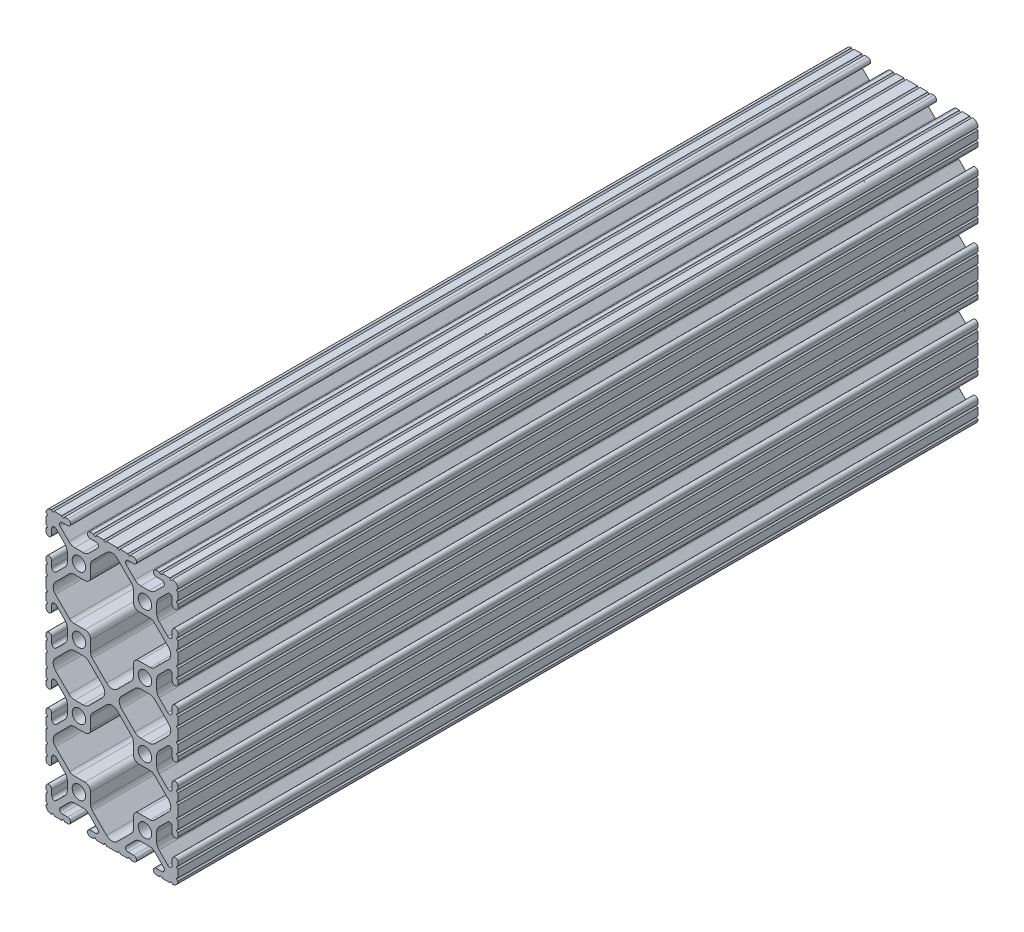
SolidWorks part; units mm, degrees
ref_plane "Front Plane" through (0, 0, 0) normal (0, 0, 1) x (1, 0, 0)
ref_plane "Top Plane" through (0, 0, 0) normal (0, 1, 0) x (1, 0, 0)
ref_plane "Right Plane" through (0, 0, 0) normal (1, 0, 0) x (0, 0, -1)
sketch "Sketch1" plane through (0, 0, 0) normal (0, 0, 1) x (1, 0, 0)
  line L0 (2.286, 55.2958) -> (-2.0184, 55.2958)
  line L1 (-3.5809, 55.943) -> (-9.0725, 61.4345)
  line L2 (-9.0725, 65.5655) -> (-3.5809, 71.057)
  line L3 (-2.0184, 71.7042) -> (2.286, 71.7042)
  line L4 (4.4958, 73.914) -> (4.4958, 78.2184)
  line L5 (5.143, 79.7809) -> (10.6345, 85.2725)
  line L6 (14.7655, 85.2725) -> (20.257, 79.7809)
  line L7 (20.9042, 78.2184) -> (20.9042, 73.914)
  line L8 (23.114, 71.7042) -> (27.4184, 71.7042)
  line L9 (28.9809, 71.057) -> (34.4725, 65.5655)
  line L10 (34.4725, 61.4345) -> (28.9809, 55.943)
  line L11 (27.4184, 55.2958) -> (23.114, 55.2958)
  line L12 (20.9042, 53.086) -> (20.9042, 48.7816)
  line L13 (20.257, 47.2191) -> (14.7655, 41.7275)
  line L14 (10.6345, 41.7275) -> (5.143, 47.2191)
  line L15 (4.4958, 48.7816) -> (4.4958, 53.086)
  line L16 (4.4958, 23.114) -> (4.4958, 27.4184)
  line L17 (5.143, 28.9809) -> (10.6345, 34.4725)
  line L18 (14.7655, 34.4725) -> (20.257, 28.9809)
  line L19 (20.9042, 27.4184) -> (20.9042, 23.114)
  line L20 (23.114, 20.9042) -> (27.4184, 20.9042)
  line L21 (28.9809, 20.257) -> (34.4725, 14.7655)
  line L22 (34.4725, 10.6345) -> (28.9809, 5.143)
  line L23 (27.4184, 4.4958) -> (23.114, 4.4958)
  line L24 (20.9042, 2.286) -> (20.9042, -2.0184)
  line L25 (20.257, -3.5809) -> (14.7655, -9.0725)
  line L26 (10.6345, -9.0725) -> (5.143, -3.5809)
  line L27 (4.4958, -2.0184) -> (4.4958, 2.286)
  line L28 (2.286, 4.4958) -> (-2.0184, 4.4958)
  line L29 (-3.5809, 5.143) -> (-9.0725, 10.6345)
  line L30 (-9.0725, 14.7655) -> (-3.5809, 20.257)
  line L31 (-2.0184, 20.9042) -> (2.286, 20.9042)
  line L32 (27.0186, 29.8958) -> (23.7824, 29.8958)
  line L33 (21.5373, 30.8258) -> (16.3286, 36.0346)
  line L34 (16.3286, 40.1654) -> (21.5373, 45.3742)
  line L35 (23.7824, 46.3042) -> (27.0186, 46.3042)
  line L36 (29.2636, 45.3743) -> (34.4725, 40.1655)
  line L37 (34.4725, 36.0345) -> (29.2636, 30.8257)
  line L38 (1.6176, 29.8958) -> (-1.6186, 29.8958)
  line L39 (-3.8636, 30.8257) -> (-9.0725, 36.0345)
  line L40 (-9.0725, 40.1655) -> (-3.8636, 45.3743)
  line L41 (-1.6186, 46.3042) -> (1.6176, 46.3042)
  line L42 (3.8627, 45.3742) -> (9.0714, 40.1654)
  line L43 (9.0714, 36.0346) -> (3.8627, 30.8258)
  line L44 (-12.7, 40.2336) -> (-12.7, 35.9664)
  line L45 (-12.7, 34.9504) -> (-12.7, 32.004)
  line L46 (-12.7, 30.988) -> (-12.7, 29.7434)
  line L47 (-10.4902, 29.7434) -> (-10.4902, 31.8743)
  line L48 (-8.7558, 32.5927) -> (-5.4258, 29.2627)
  line L49 (-4.4958, 27.0176) -> (-4.4958, 23.7824)
  line L50 (-5.4258, 21.5373) -> (-8.7558, 18.2073)
  line L51 (-10.4902, 18.9257) -> (-10.4902, 21.0566)
  line L52 (-12.7, 21.0566) -> (-12.7, 19.812)
  line L53 (-12.7, 18.796) -> (-12.7, 15.8496)
  line L54 (-12.7, 14.8336) -> (-12.7, 10.5664)
  line L55 (-12.7, 9.5504) -> (-12.7, 6.604)
  line L56 (-12.7, 5.588) -> (-12.7, 4.3434)
  line L57 (-10.4902, 4.3434) -> (-10.4902, 6.4743)
  line L58 (-8.7558, 7.1927) -> (-5.4258, 3.8627)
  line L59 (-4.4958, 1.6176) -> (-4.4958, -1.6176)
  line L60 (-5.4258, -3.8627) -> (-8.7558, -7.1927)
  line L61 (-10.4902, -6.4743) -> (-10.4902, -4.3434)
  line L62 (-12.7, -4.3434) -> (-12.7, -5.588)
  line L63 (-12.7, -6.604) -> (-12.7, -9.5504)
  line L64 (-9.5504, -12.7) -> (-6.604, -12.7)
  line L65 (-5.588, -12.7) -> (-4.3434, -12.7)
  line L66 (-4.3434, -10.4902) -> (-6.4743, -10.4902)
  line L67 (-7.1927, -8.7558) -> (-3.8627, -5.4258)
  line L68 (-1.6176, -4.4958) -> (1.6176, -4.4958)
  line L69 (3.8627, -5.4258) -> (7.1927, -8.7558)
  line L70 (6.4743, -10.4902) -> (4.3434, -10.4902)
  line L71 (4.3434, -12.7) -> (5.588, -12.7)
  line L72 (6.604, -12.7) -> (9.5504, -12.7)
  line L73 (10.5664, -12.7) -> (14.8336, -12.7)
  line L74 (15.8496, -12.7) -> (18.796, -12.7)
  line L75 (19.812, -12.7) -> (21.0566, -12.7)
  line L76 (21.0566, -10.4902) -> (18.9257, -10.4902)
  line L77 (18.2073, -8.7558) -> (21.5373, -5.4258)
  line L78 (23.7824, -4.4958) -> (27.0176, -4.4958)
  line L79 (29.2627, -5.4258) -> (32.5927, -8.7558)
  line L80 (31.8743, -10.4902) -> (29.7434, -10.4902)
  line L81 (29.7434, -12.7) -> (30.988, -12.7)
  line L82 (32.004, -12.7) -> (34.9504, -12.7)
  line L83 (38.1, -9.5504) -> (38.1, -6.604)
  line L84 (38.1, -5.588) -> (38.1, -4.3434)
  line L85 (35.8902, -4.3434) -> (35.8902, -6.4743)
  line L86 (34.1558, -7.1927) -> (30.8258, -3.8627)
  line L87 (29.8958, -1.6176) -> (29.8958, 1.6176)
  line L88 (30.8258, 3.8627) -> (34.1558, 7.1927)
  line L89 (35.8902, 6.4743) -> (35.8902, 4.3434)
  line L90 (38.1, 4.3434) -> (38.1, 5.588)
  line L91 (38.1, 6.604) -> (38.1, 9.5504)
  line L92 (38.1, 10.5664) -> (38.1, 14.8336)
  line L93 (38.1, 15.8496) -> (38.1, 18.796)
  line L94 (38.1, 19.812) -> (38.1, 21.0566)
  line L95 (35.8902, 21.0566) -> (35.8902, 18.9257)
  line L96 (34.1558, 18.2073) -> (30.8258, 21.5373)
  line L97 (29.8958, 23.7824) -> (29.8958, 27.0176)
  line L98 (30.8258, 29.2627) -> (34.1558, 32.5927)
  line L99 (35.8902, 31.8743) -> (35.8902, 29.7434)
  line L100 (38.1, 29.7434) -> (38.1, 30.988)
  line L101 (38.1, 32.004) -> (38.1, 34.9504)
  line L102 (38.1, 35.9664) -> (38.1, 40.2336)
  line L103 (38.1, 41.2496) -> (38.1, 44.196)
  line L104 (38.1, 45.212) -> (38.1, 46.4566)
  line L105 (35.8902, 46.4566) -> (35.8902, 44.3257)
  line L106 (34.1558, 43.6073) -> (30.8258, 46.9373)
  line L107 (29.8958, 49.1824) -> (29.8958, 52.4176)
  line L108 (30.8258, 54.6627) -> (34.1558, 57.9927)
  line L109 (35.8902, 57.2743) -> (35.8902, 55.1434)
  line L110 (38.1, 55.1434) -> (38.1, 56.388)
  line L111 (38.1, 57.404) -> (38.1, 60.3504)
  line L112 (38.1, 61.3664) -> (38.1, 65.6336)
  line L113 (38.1, 66.6496) -> (38.1, 69.596)
  line L114 (38.1, 70.612) -> (38.1, 71.8566)
  line L115 (35.8902, 71.8566) -> (35.8902, 69.7257)
  line L116 (34.1558, 69.0073) -> (30.8258, 72.3373)
  line L117 (29.8958, 74.5824) -> (29.8958, 77.8176)
  line L118 (30.8258, 80.0627) -> (34.1558, 83.3927)
  line L119 (35.8902, 82.6743) -> (35.8902, 80.5434)
  line L120 (38.1, 80.5434) -> (38.1, 81.788)
  line L121 (38.1, 82.804) -> (38.1, 85.7504)
  line L122 (34.9504, 88.9) -> (32.004, 88.9)
  line L123 (30.988, 88.9) -> (29.7434, 88.9)
  line L124 (29.7434, 86.6902) -> (31.8743, 86.6902)
  line L125 (32.5927, 84.9558) -> (29.2627, 81.6258)
  line L126 (27.0176, 80.6958) -> (23.7824, 80.6958)
  line L127 (21.5373, 81.6258) -> (18.2073, 84.9558)
  line L128 (18.9257, 86.6902) -> (21.0566, 86.6902)
  line L129 (21.0566, 88.9) -> (19.812, 88.9)
  line L130 (18.796, 88.9) -> (15.8496, 88.9)
  line L131 (14.8336, 88.9) -> (10.5664, 88.9)
  line L132 (9.5504, 88.9) -> (6.604, 88.9)
  line L133 (5.588, 88.9) -> (4.3434, 88.9)
  line L134 (4.3434, 86.6902) -> (6.4743, 86.6902)
  line L135 (7.1927, 84.9558) -> (3.8627, 81.6258)
  line L136 (1.6176, 80.6958) -> (-1.6176, 80.6958)
  line L137 (-3.8627, 81.6258) -> (-7.1927, 84.9558)
  line L138 (-6.4743, 86.6902) -> (-4.3434, 86.6902)
  line L139 (-4.3434, 88.9) -> (-5.588, 88.9)
  line L140 (-6.604, 88.9) -> (-9.5504, 88.9)
  line L141 (-12.7, 85.7504) -> (-12.7, 82.804)
  line L142 (-12.7, 81.788) -> (-12.7, 80.5434)
  line L143 (-10.4902, 80.5434) -> (-10.4902, 82.6743)
  line L144 (-8.7558, 83.3927) -> (-5.4258, 80.0627)
  line L145 (-4.4958, 77.8176) -> (-4.4958, 74.5824)
  line L146 (-5.4258, 72.3373) -> (-8.7558, 69.0073)
  line L147 (-10.4902, 69.7257) -> (-10.4902, 71.8566)
  line L148 (-12.7, 71.8566) -> (-12.7, 70.612)
  line L149 (-12.7, 69.596) -> (-12.7, 66.6496)
  line L150 (-12.7, 65.6336) -> (-12.7, 61.3664)
  line L151 (-12.7, 60.3504) -> (-12.7, 57.404)
  line L152 (-12.7, 56.388) -> (-12.7, 55.1434)
  line L153 (-10.4902, 55.1434) -> (-10.4902, 57.2743)
  line L154 (-8.7558, 57.9927) -> (-5.4258, 54.6627)
  line L155 (-4.4958, 52.4176) -> (-4.4958, 49.1824)
  line L156 (-5.4258, 46.9373) -> (-8.7558, 43.6073)
  line L157 (-10.4902, 44.3257) -> (-10.4902, 46.4566)
  line L158 (-12.7, 46.4566) -> (-12.7, 45.212)
  line L159 (-12.7, 44.196) -> (-12.7, 41.2496)
  arc A0 (4.4958, 53.086) -> (2.286, 55.2958) centre (2.286, 53.086) ccw
  arc A1 (-3.5809, 55.943) -> (-2.0184, 55.2958) centre (-2.0184, 57.5056) ccw
  arc A2 (-9.0725, 65.5655) -> (-9.0725, 61.4345) centre (-7.0071, 63.5) ccw
  arc A3 (-2.0184, 71.7042) -> (-3.5809, 71.057) centre (-2.0184, 69.4944) ccw
  arc A4 (2.286, 71.7042) -> (4.4958, 73.914) centre (2.286, 73.914) ccw
  arc A5 (5.143, 79.7809) -> (4.4958, 78.2184) centre (6.7056, 78.2184) ccw
  arc A6 (14.7655, 85.2725) -> (10.6345, 85.2725) centre (12.7, 83.2071) ccw
  arc A7 (20.9042, 78.2184) -> (20.257, 79.7809) centre (18.6944, 78.2184) ccw
  arc A8 (20.9042, 73.914) -> (23.114, 71.7042) centre (23.114, 73.914) ccw
  arc A9 (28.9809, 71.057) -> (27.4184, 71.7042) centre (27.4184, 69.4944) ccw
  arc A10 (34.4725, 61.4345) -> (34.4725, 65.5655) centre (32.4071, 63.5) ccw
  arc A11 (27.4184, 55.2958) -> (28.9809, 55.943) centre (27.4184, 57.5056) ccw
  arc A12 (23.114, 55.2958) -> (20.9042, 53.086) centre (23.114, 53.086) ccw
  arc A13 (20.257, 47.2191) -> (20.9042, 48.7816) centre (18.6944, 48.7816) ccw
  arc A14 (10.6345, 41.7275) -> (14.7655, 41.7275) centre (12.7, 43.7929) ccw
  arc A15 (4.4958, 48.7816) -> (5.143, 47.2191) centre (6.7056, 48.7816) ccw
  arc A16 (2.286, 20.9042) -> (4.4958, 23.114) centre (2.286, 23.114) ccw
  arc A17 (5.143, 28.9809) -> (4.4958, 27.4184) centre (6.7056, 27.4184) ccw
  arc A18 (14.7655, 34.4725) -> (10.6345, 34.4725) centre (12.7, 32.4071) ccw
  arc A19 (20.9042, 27.4184) -> (20.257, 28.9809) centre (18.6944, 27.4184) ccw
  arc A20 (20.9042, 23.114) -> (23.114, 20.9042) centre (23.114, 23.114) ccw
  arc A21 (28.9809, 20.257) -> (27.4184, 20.9042) centre (27.4184, 18.6944) ccw
  arc A22 (34.4725, 10.6345) -> (34.4725, 14.7655) centre (32.4071, 12.7) ccw
  arc A23 (27.4184, 4.4958) -> (28.9809, 5.143) centre (27.4184, 6.7056) ccw
  arc A24 (23.114, 4.4958) -> (20.9042, 2.286) centre (23.114, 2.286) ccw
  arc A25 (20.257, -3.5809) -> (20.9042, -2.0184) centre (18.6944, -2.0184) ccw
  arc A26 (10.6345, -9.0725) -> (14.7655, -9.0725) centre (12.7, -7.0071) ccw
  arc A27 (4.4958, -2.0184) -> (5.143, -3.5809) centre (6.7056, -2.0184) ccw
  arc A28 (4.4958, 2.286) -> (2.286, 4.4958) centre (2.286, 2.286) ccw
  arc A29 (-3.5809, 5.143) -> (-2.0184, 4.4958) centre (-2.0184, 6.7056) ccw
  arc A30 (-9.0725, 14.7655) -> (-9.0725, 10.6345) centre (-7.0071, 12.7) ccw
  arc A31 (-2.0184, 20.9042) -> (-3.5809, 20.257) centre (-2.0184, 18.6944) ccw
  arc A32 (27.0186, 29.8958) -> (29.2636, 30.8257) centre (27.0186, 33.0708) ccw
  arc A33 (21.5373, 30.8258) -> (23.7824, 29.8958) centre (23.7824, 33.0708) ccw
  arc A34 (16.3286, 40.1654) -> (16.3286, 36.0346) centre (18.3941, 38.1) ccw
  arc A35 (23.7824, 46.3042) -> (21.5373, 45.3742) centre (23.7824, 43.1292) ccw
  arc A36 (29.2636, 45.3743) -> (27.0186, 46.3042) centre (27.0186, 43.1292) ccw
  arc A37 (34.4725, 36.0345) -> (34.4725, 40.1655) centre (32.4071, 38.1) ccw
  arc A38 (1.6176, 29.8958) -> (3.8627, 30.8258) centre (1.6176, 33.0708) ccw
  arc A39 (-3.8636, 30.8257) -> (-1.6186, 29.8958) centre (-1.6186, 33.0708) ccw
  arc A40 (-9.0725, 40.1655) -> (-9.0725, 36.0345) centre (-7.0071, 38.1) ccw
  arc A41 (-1.6186, 46.3042) -> (-3.8636, 45.3743) centre (-1.6186, 43.1292) ccw
  arc A42 (3.8627, 45.3742) -> (1.6176, 46.3042) centre (1.6176, 43.1292) ccw
  arc A43 (9.0714, 36.0346) -> (9.0714, 40.1654) centre (7.0059, 38.1) ccw
  circle A44 centre (25.4, 76.2) radius 2.6035
  circle A45 centre (0, 76.2) radius 2.6035
  circle A46 centre (25.4, 50.8) radius 2.6035
  circle A47 centre (0, 50.8) radius 2.6035
  circle A48 centre (25.4, 0) radius 2.6035
  circle A49 centre (0, 0) radius 2.6035
  circle A50 centre (25.4, 25.4) radius 2.6035
  circle A51 centre (0, 25.4) radius 2.6035
  arc A52 (-12.7, 34.9504) -> (-12.7, 35.9664) centre (-12.7, 35.4584) ccw
  arc A53 (-12.7, 30.988) -> (-12.7, 32.004) centre (-12.7, 31.496) ccw
  arc A54 (-12.7, 29.7434) -> (-10.4902, 29.7434) centre (-11.5951, 29.7434) ccw
  arc A55 (-8.7558, 32.5927) -> (-10.4902, 31.8743) centre (-9.4742, 31.8743) ccw
  arc A56 (-4.4958, 27.0176) -> (-5.4258, 29.2627) centre (-7.6708, 27.0176) ccw
  arc A57 (-5.4258, 21.5373) -> (-4.4958, 23.7824) centre (-7.6708, 23.7824) ccw
  arc A58 (-10.4902, 18.9257) -> (-8.7558, 18.2073) centre (-9.4742, 18.9257) ccw
  arc A59 (-10.4902, 21.0566) -> (-12.7, 21.0566) centre (-11.5951, 21.0566) ccw
  arc A60 (-12.7, 18.796) -> (-12.7, 19.812) centre (-12.7, 19.304) ccw
  arc A61 (-12.7, 14.8336) -> (-12.7, 15.8496) centre (-12.7, 15.3416) ccw
  arc A62 (-12.7, 9.5504) -> (-12.7, 10.5664) centre (-12.7, 10.0584) ccw
  arc A63 (-12.7, 5.588) -> (-12.7, 6.604) centre (-12.7, 6.096) ccw
  arc A64 (-12.7, 4.3434) -> (-10.4902, 4.3434) centre (-11.5951, 4.3434) ccw
  arc A65 (-8.7558, 7.1927) -> (-10.4902, 6.4743) centre (-9.4742, 6.4743) ccw
  arc A66 (-4.4958, 1.6176) -> (-5.4258, 3.8627) centre (-7.6708, 1.6176) ccw
  arc A67 (-5.4258, -3.8627) -> (-4.4958, -1.6176) centre (-7.6708, -1.6176) ccw
  arc A68 (-10.4902, -6.4743) -> (-8.7558, -7.1927) centre (-9.4742, -6.4743) ccw
  arc A69 (-10.4902, -4.3434) -> (-12.7, -4.3434) centre (-11.5951, -4.3434) ccw
  arc A70 (-12.7, -6.604) -> (-12.7, -5.588) centre (-12.7, -6.096) ccw
  arc A71 (-12.6998, -10.5664) -> (-12.7, -9.5504) centre (-12.7, -10.0584) ccw
  arc A72 (-12.6998, -10.5664) -> (-10.5664, -12.6998) centre (-10.5918, -10.5918) ccw
  arc A73 (-9.5504, -12.7) -> (-10.5664, -12.6998) centre (-10.0584, -12.7) ccw
  arc A74 (-5.588, -12.7) -> (-6.604, -12.7) centre (-6.096, -12.7) ccw
  arc A75 (-4.3434, -12.7) -> (-4.3434, -10.4902) centre (-4.3434, -11.5951) ccw
  arc A76 (-7.1927, -8.7558) -> (-6.4743, -10.4902) centre (-6.4743, -9.4742) ccw
  arc A77 (-1.6176, -4.4958) -> (-3.8627, -5.4258) centre (-1.6176, -7.6708) ccw
  arc A78 (3.8627, -5.4258) -> (1.6176, -4.4958) centre (1.6176, -7.6708) ccw
  arc A79 (6.4743, -10.4902) -> (7.1927, -8.7558) centre (6.4743, -9.4742) ccw
  arc A80 (4.3434, -10.4902) -> (4.3434, -12.7) centre (4.3434, -11.5951) ccw
  arc A81 (6.604, -12.7) -> (5.588, -12.7) centre (6.096, -12.7) ccw
  arc A82 (10.5664, -12.7) -> (9.5504, -12.7) centre (10.0584, -12.7) ccw
  arc A83 (15.8496, -12.7) -> (14.8336, -12.7) centre (15.3416, -12.7) ccw
  arc A84 (19.812, -12.7) -> (18.796, -12.7) centre (19.304, -12.7) ccw
  arc A85 (21.0566, -12.7) -> (21.0566, -10.4902) centre (21.0566, -11.5951) ccw
  arc A86 (18.2073, -8.7558) -> (18.9257, -10.4902) centre (18.9257, -9.4742) ccw
  arc A87 (23.7824, -4.4958) -> (21.5373, -5.4258) centre (23.7824, -7.6708) ccw
  arc A88 (29.2627, -5.4258) -> (27.0176, -4.4958) centre (27.0176, -7.6708) ccw
  arc A89 (31.8743, -10.4902) -> (32.5927, -8.7558) centre (31.8743, -9.4742) ccw
  arc A90 (29.7434, -10.4902) -> (29.7434, -12.7) centre (29.7434, -11.5951) ccw
  arc A91 (32.004, -12.7) -> (30.988, -12.7) centre (31.496, -12.7) ccw
  arc A92 (35.9664, -12.6998) -> (34.9504, -12.7) centre (35.4584, -12.7) ccw
  arc A93 (35.9664, -12.6998) -> (38.0998, -10.5664) centre (35.9918, -10.5918) ccw
  arc A94 (38.1, -9.5504) -> (38.0998, -10.5664) centre (38.1, -10.0584) ccw
  arc A95 (38.1, -5.588) -> (38.1, -6.604) centre (38.1, -6.096) ccw
  arc A96 (38.1, -4.3434) -> (35.8902, -4.3434) centre (36.9951, -4.3434) ccw
  arc A97 (34.1558, -7.1927) -> (35.8902, -6.4743) centre (34.8742, -6.4743) ccw
  arc A98 (29.8958, -1.6176) -> (30.8258, -3.8627) centre (33.0708, -1.6176) ccw
  arc A99 (30.8258, 3.8627) -> (29.8958, 1.6176) centre (33.0708, 1.6176) ccw
  arc A100 (35.8902, 6.4743) -> (34.1558, 7.1927) centre (34.8742, 6.4743) ccw
  arc A101 (35.8902, 4.3434) -> (38.1, 4.3434) centre (36.9951, 4.3434) ccw
  arc A102 (38.1, 6.604) -> (38.1, 5.588) centre (38.1, 6.096) ccw
  arc A103 (38.1, 10.5664) -> (38.1, 9.5504) centre (38.1, 10.0584) ccw
  arc A104 (38.1, 15.8496) -> (38.1, 14.8336) centre (38.1, 15.3416) ccw
  arc A105 (38.1, 19.812) -> (38.1, 18.796) centre (38.1, 19.304) ccw
  arc A106 (38.1, 21.0566) -> (35.8902, 21.0566) centre (36.9951, 21.0566) ccw
  arc A107 (34.1558, 18.2073) -> (35.8902, 18.9257) centre (34.8742, 18.9257) ccw
  arc A108 (29.8958, 23.7824) -> (30.8258, 21.5373) centre (33.0708, 23.7824) ccw
  arc A109 (30.8258, 29.2627) -> (29.8958, 27.0176) centre (33.0708, 27.0176) ccw
  arc A110 (35.8902, 31.8743) -> (34.1558, 32.5927) centre (34.8742, 31.8743) ccw
  arc A111 (35.8902, 29.7434) -> (38.1, 29.7434) centre (36.9951, 29.7434) ccw
  arc A112 (38.1, 32.004) -> (38.1, 30.988) centre (38.1, 31.496) ccw
  arc A113 (38.1, 35.9664) -> (38.1, 34.9504) centre (38.1, 35.4584) ccw
  arc A114 (38.1, 41.2496) -> (38.1, 40.2336) centre (38.1, 40.7416) ccw
  arc A115 (38.1, 45.212) -> (38.1, 44.196) centre (38.1, 44.704) ccw
  arc A116 (38.1, 46.4566) -> (35.8902, 46.4566) centre (36.9951, 46.4566) ccw
  arc A117 (34.1558, 43.6073) -> (35.8902, 44.3257) centre (34.8742, 44.3257) ccw
  arc A118 (29.8958, 49.1824) -> (30.8258, 46.9373) centre (33.0708, 49.1824) ccw
  arc A119 (30.8258, 54.6627) -> (29.8958, 52.4176) centre (33.0708, 52.4176) ccw
  arc A120 (35.8902, 57.2743) -> (34.1558, 57.9927) centre (34.8742, 57.2743) ccw
  arc A121 (35.8902, 55.1434) -> (38.1, 55.1434) centre (36.9951, 55.1434) ccw
  arc A122 (38.1, 57.404) -> (38.1, 56.388) centre (38.1, 56.896) ccw
  arc A123 (38.1, 61.3664) -> (38.1, 60.3504) centre (38.1, 60.8584) ccw
  arc A124 (38.1, 66.6496) -> (38.1, 65.6336) centre (38.1, 66.1416) ccw
  arc A125 (38.1, 70.612) -> (38.1, 69.596) centre (38.1, 70.104) ccw
  arc A126 (38.1, 71.8566) -> (35.8902, 71.8566) centre (36.9951, 71.8566) ccw
  arc A127 (34.1558, 69.0073) -> (35.8902, 69.7257) centre (34.8742, 69.7257) ccw
  arc A128 (29.8958, 74.5824) -> (30.8258, 72.3373) centre (33.0708, 74.5824) ccw
  arc A129 (30.8258, 80.0627) -> (29.8958, 77.8176) centre (33.0708, 77.8176) ccw
  arc A130 (35.8902, 82.6743) -> (34.1558, 83.3927) centre (34.8742, 82.6743) ccw
  arc A131 (35.8902, 80.5434) -> (38.1, 80.5434) centre (36.9951, 80.5434) ccw
  arc A132 (38.1, 82.804) -> (38.1, 81.788) centre (38.1, 82.296) ccw
  arc A133 (38.0998, 86.7664) -> (38.1, 85.7504) centre (38.1, 86.2584) ccw
  arc A134 (38.0998, 86.7664) -> (35.9664, 88.8998) centre (35.9918, 86.7918) ccw
  arc A135 (34.9504, 88.9) -> (35.9664, 88.8998) centre (35.4584, 88.9) ccw
  arc A136 (30.988, 88.9) -> (32.004, 88.9) centre (31.496, 88.9) ccw
  arc A137 (29.7434, 88.9) -> (29.7434, 86.6902) centre (29.7434, 87.7951) ccw
  arc A138 (32.5927, 84.9558) -> (31.8743, 86.6902) centre (31.8743, 85.6742) ccw
  arc A139 (27.0176, 80.6958) -> (29.2627, 81.6258) centre (27.0176, 83.8708) ccw
  arc A140 (21.5373, 81.6258) -> (23.7824, 80.6958) centre (23.7824, 83.8708) ccw
  arc A141 (18.9257, 86.6902) -> (18.2073, 84.9558) centre (18.9257, 85.6742) ccw
  arc A142 (21.0566, 86.6902) -> (21.0566, 88.9) centre (21.0566, 87.7951) ccw
  arc A143 (18.796, 88.9) -> (19.812, 88.9) centre (19.304, 88.9) ccw
  arc A144 (14.8336, 88.9) -> (15.8496, 88.9) centre (15.3416, 88.9) ccw
  arc A145 (9.5504, 88.9) -> (10.5664, 88.9) centre (10.0584, 88.9) ccw
  arc A146 (5.588, 88.9) -> (6.604, 88.9) centre (6.096, 88.9) ccw
  arc A147 (4.3434, 88.9) -> (4.3434, 86.6902) centre (4.3434, 87.7951) ccw
  arc A148 (7.1927, 84.9558) -> (6.4743, 86.6902) centre (6.4743, 85.6742) ccw
  arc A149 (1.6176, 80.6958) -> (3.8627, 81.6258) centre (1.6176, 83.8708) ccw
  arc A150 (-3.8627, 81.6258) -> (-1.6176, 80.6958) centre (-1.6176, 83.8708) ccw
  arc A151 (-6.4743, 86.6902) -> (-7.1927, 84.9558) centre (-6.4743, 85.6742) ccw
  arc A152 (-4.3434, 86.6902) -> (-4.3434, 88.9) centre (-4.3434, 87.7951) ccw
  arc A153 (-6.604, 88.9) -> (-5.588, 88.9) centre (-6.096, 88.9) ccw
  arc A154 (-10.5664, 88.8998) -> (-9.5504, 88.9) centre (-10.0584, 88.9) ccw
  arc A155 (-10.5664, 88.8998) -> (-12.6998, 86.7664) centre (-10.5918, 86.7918) ccw
  arc A156 (-12.7, 85.7504) -> (-12.6998, 86.7664) centre (-12.7, 86.2584) ccw
  arc A157 (-12.7, 81.788) -> (-12.7, 82.804) centre (-12.7, 82.296) ccw
  arc A158 (-12.7, 80.5434) -> (-10.4902, 80.5434) centre (-11.5951, 80.5434) ccw
  arc A159 (-8.7558, 83.3927) -> (-10.4902, 82.6743) centre (-9.4742, 82.6743) ccw
  arc A160 (-4.4958, 77.8176) -> (-5.4258, 80.0627) centre (-7.6708, 77.8176) ccw
  arc A161 (-5.4258, 72.3373) -> (-4.4958, 74.5824) centre (-7.6708, 74.5824) ccw
  arc A162 (-10.4902, 69.7257) -> (-8.7558, 69.0073) centre (-9.4742, 69.7257) ccw
  arc A163 (-10.4902, 71.8566) -> (-12.7, 71.8566) centre (-11.5951, 71.8566) ccw
  arc A164 (-12.7, 69.596) -> (-12.7, 70.612) centre (-12.7, 70.104) ccw
  arc A165 (-12.7, 65.6336) -> (-12.7, 66.6496) centre (-12.7, 66.1416) ccw
  arc A166 (-12.7, 60.3504) -> (-12.7, 61.3664) centre (-12.7, 60.8584) ccw
  arc A167 (-12.7, 56.388) -> (-12.7, 57.404) centre (-12.7, 56.896) ccw
  arc A168 (-12.7, 55.1434) -> (-10.4902, 55.1434) centre (-11.5951, 55.1434) ccw
  arc A169 (-8.7558, 57.9927) -> (-10.4902, 57.2743) centre (-9.4742, 57.2743) ccw
  arc A170 (-4.4958, 52.4176) -> (-5.4258, 54.6627) centre (-7.6708, 52.4176) ccw
  arc A171 (-5.4258, 46.9373) -> (-4.4958, 49.1824) centre (-7.6708, 49.1824) ccw
  arc A172 (-10.4902, 44.3257) -> (-8.7558, 43.6073) centre (-9.4742, 44.3257) ccw
  arc A173 (-10.4902, 46.4566) -> (-12.7, 46.4566) centre (-11.5951, 46.4566) ccw
  arc A174 (-12.7, 44.196) -> (-12.7, 45.212) centre (-12.7, 44.704) ccw
  arc A175 (-12.7, 40.2336) -> (-12.7, 41.2496) centre (-12.7, 40.7416) ccw
extrude "Extrude1" add sketch "Sketch1" against normal blind 307.975
